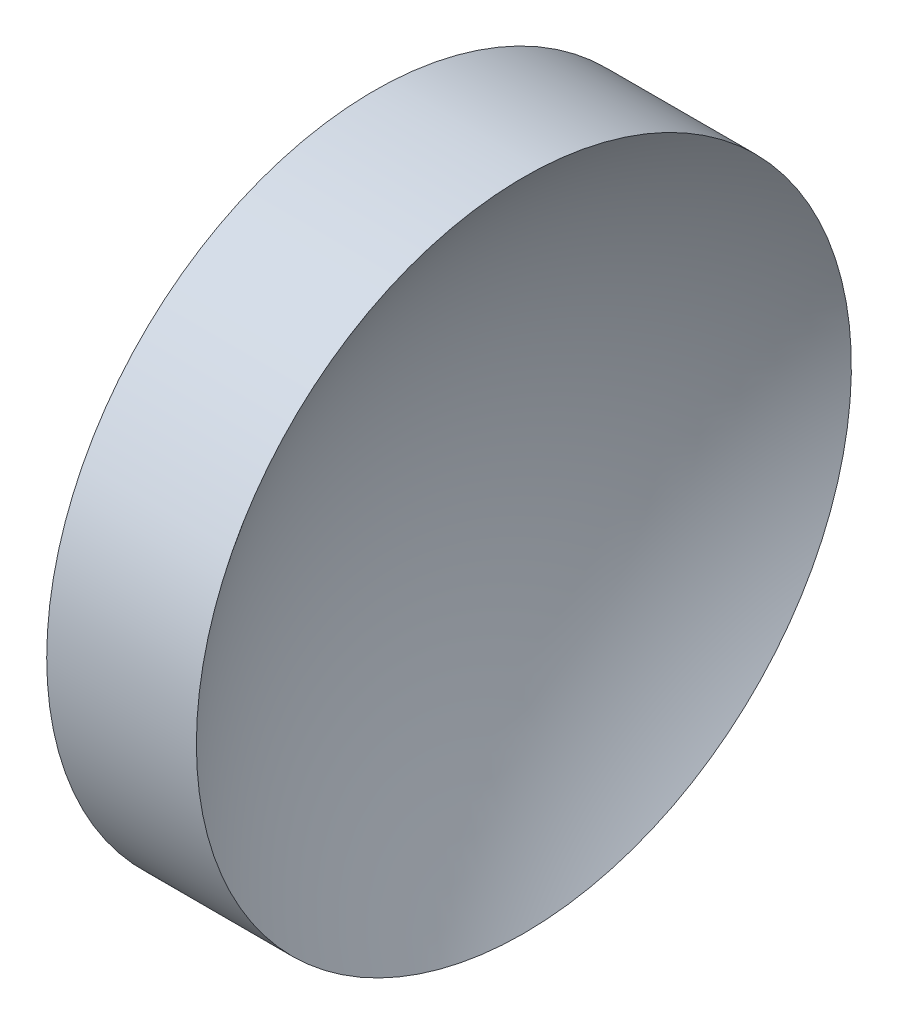
SolidWorks part; units mm, degrees
ref_plane "前视基准面" through (0, 0, 0) normal (0, 0, 1) x (1, 0, 0)
ref_plane "上视基准面" through (0, 0, 0) normal (0, 1, 0) x (1, 0, 0)
ref_plane "右视基准面" through (0, 0, 0) normal (1, 0, 0) x (0, 0, -1)
sketch "草图1" plane through (0, 0, 0) normal (0, 0, 1) x (1, 0, 0)
  line L0 (105.6218, 65.1556) -> (137.1869, 65.1556) construction
  line L1 (113.7394, 65.1556) -> (113.7394, 90.1556)
  line L2 (113.7394, 90.1556) -> (125.1656, 90.1556)
  line L3 (116.7394, 65.1556) -> (113.7394, 65.1556)
  arc A0 (125.1656, 90.1556) -> (116.7394, 65.1556) centre (158.0394, 65.1556) ccw
revolve "旋转1" add sketch "草图1" angle 360 about L0
